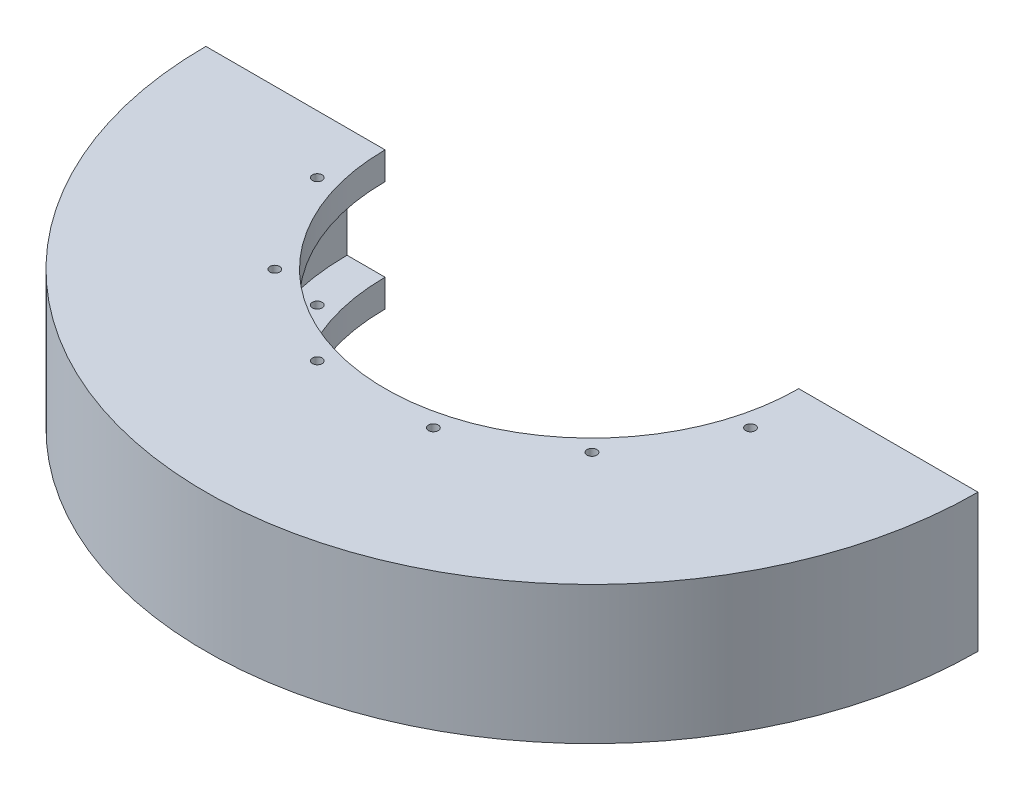
SolidWorks part; units mm, degrees
ref_plane "Front Plane" through (0, 0, 0) normal (0, 0, 1) x (1, 0, 0)
ref_plane "Top Plane" through (0, 0, 0) normal (0, 1, 0) x (1, 0, 0)
ref_plane "Right Plane" through (0, 0, 0) normal (1, 0, 0) x (0, 0, -1)
sketch "Sketch1" plane through (0, 0, 0) normal (0, 0, 1) x (1, 0, 0)
  line L0 (0, 0) -> (56.388, 0) construction
  line L1 (56.388, 0) -> (56.388, 9.525)
  line L2 (56.388, 0) -> (56.388, -9.525)
  line L3 (56.388, 9.525) -> (47.625, 9.525)
  line L4 (56.388, -9.525) -> (47.625, -9.525)
  line L5 (47.625, 9.525) -> (47.625, 15.875)
  line L6 (47.625, 15.875) -> (88.9, 15.875)
  line L7 (47.625, -9.525) -> (47.625, -15.875)
  line L8 (47.625, -15.875) -> (88.9, -15.875)
  line L9 (88.9, 15.875) -> (88.9, -15.875)
  line L10 (0, 22.5393) -> (0, -21.157) construction
  dimension "D1" = 56.388
  dimension "D2" = 9.525
  dimension "D3" = 9.525
  dimension "D4" = 47.625
  dimension "D5" = 6.35
  dimension "D6" = 6.35
  dimension "D7" = 88.9
  dimension "D8" = 47.625
revolve "Revolve1" add sketch "Sketch1" angle 180 about L10
sketch "Sketch2" plane through (0, 15.875, 0) normal (0, 1, 0) x (1, 0, 0)
  line L0 (49.8787, -13.3649) -> (0, 0) construction
  line L1 (0, 0) -> (55.1424, 0) construction
  line L2 (88.9, 0) -> (47.625, 0) construction
  point P4 (49.8787, -13.3649)
  dimension "D1" = 15
  dimension "D2" = 51.6382
hole_wizard "Tap Drill for #4-40 Tap1" positions "3DSketch1" profile "Sketch3" hole size "#4-40" standard "ANSI Inch" end condition through all
sketch3d "3DSketch1"
  point P0 (49.8787, 15.875, 13.3649)
sketch "Sketch3" plane through (49.8787, 15.875, 13.3649) normal (1, 0, 0) x (0, 0, 1)
  line L0 (0, 0) -> (0, 31.75)
  line L1 (0, 31.75) -> (1.1303, 31.75)
  line L2 (1.1303, 31.75) -> (1.1303, 0)
  line L5 (1.1303, 0) -> (0, 0)
  line L11 (0, -6.35) -> (0, 107.95) construction
  dimension "Thru Hole Dia." = 2.2606
  dimension "Thru Hole Depth" = 31.75
pattern_circular "CirPattern1" count 12 over 360 about axis through (0, 15.875, 0) along (0, 1, 0) skipping 1, 2, 3, 4, 5, 6 of "Tap Drill for #4-40 Tap1"
